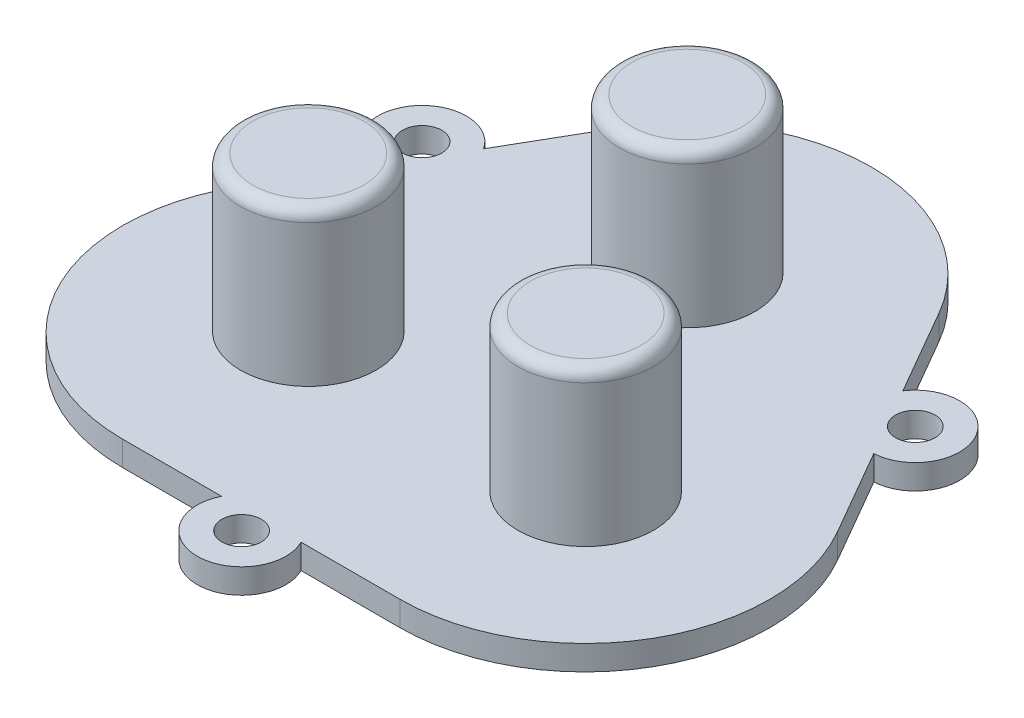
SolidWorks part; units mm, degrees
ref_plane "Front Plane" through (0, 0, 0) normal (0, 0, 1) x (1, 0, 0)
ref_plane "Top Plane" through (0, 0, 0) normal (0, 1, 0) x (1, 0, 0)
ref_plane "Right Plane" through (0, 0, 0) normal (1, 0, 0) x (0, 0, -1)
sketch "Sketch5" plane through (0, 0, 0) normal (0, 1, 0) x (1, 0, 0)
  line L3 (-11.25, -22.1428) -> (-3.2249, -22.1428)
  line L4 (3.2249, -22.1428) -> (11.25, -22.1428)
  line L5 (24.2404, 0.3572) -> (20.2278, 7.3072)
  line L6 (17.0029, 12.8928) -> (12.9904, 19.8428)
  line L7 (-12.9904, 19.8428) -> (-17.0029, 12.8928)
  line L8 (-20.2278, 7.3072) -> (-24.2404, 0.3572)
  arc A3 (-3.2249, -22.1428) -> (3.2249, -22.1428) centre (0, -23.7428) ccw
  arc A4 (11.25, -22.1428) -> (24.2404, 0.3572) centre (11.25, -7.1428) ccw
  arc A5 (20.2278, 7.3072) -> (17.0029, 12.8928) centre (20.001, 10.9) ccw
  arc A6 (12.9904, 19.8428) -> (-12.9904, 19.8428) centre (0, 12.3428) ccw
  arc A7 (-17.0029, 12.8928) -> (-20.2278, 7.3072) centre (-20.001, 10.9) ccw
  arc A8 (-24.2404, 0.3572) -> (-11.25, -22.1428) centre (-11.25, -7.1428) ccw
  circle A9 centre (20.001, 10.9) radius 1.6
  circle A10 centre (0, -23.7428) radius 1.6
  circle A11 centre (-20.001, 10.9) radius 1.6
extrude "Boss-Extrude2" add sketch "Sketch5" along normal blind 2
sketch "Sketch6" plane through (0, 0, 0) normal (0, 1, 0) x (1, 0, 0)
  circle A12 centre (-0.06, 12.4628) radius 5.5
  circle A13 centre (11.19, -7.0227) radius 5.5
  circle A14 centre (-11.31, -7.0227) radius 5.5
  dimension "D1" = 11
extrude "Boss-Extrude3" add sketch "Sketch6" along normal blind 14.5
fillet "Fillet1" radius 1 3 edges at (-11.31, 14.5, 12.5227) (11.19, 14.5, 12.5227) (-0.06, 14.5, -6.9628)
sketch "Sketch7" plane through (-18.335, 0, -10.5857) normal (-0.866, 0, -0.5) x (-0.5, 0, 0.866)
  circle A0 centre (-9.601, 1) radius 0.5
  circle A1 centre (-7.601, 1) radius 0.5
  dimension "D1" = 1
  dimension "D2" = 2
extrude "Boss-Extrude4" add sketch "Sketch7" along normal blind 0.6
